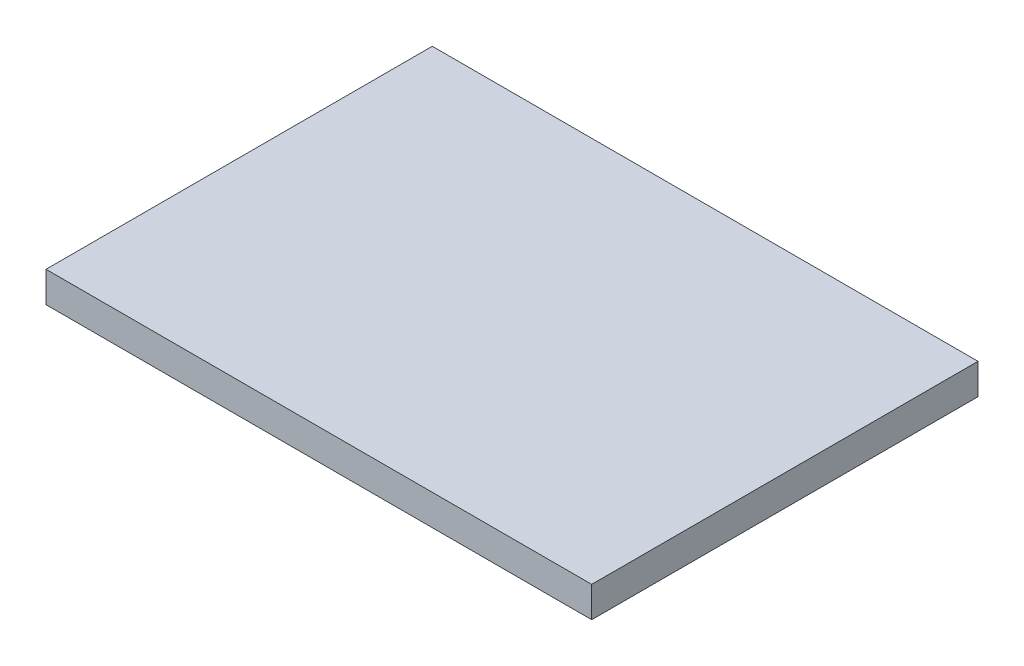
SolidWorks part; units mm, degrees
ref_plane "Front Plane" through (0, 0, 0) normal (0, 0, 1) x (1, 0, 0)
ref_plane "Top Plane" through (0, 0, 0) normal (0, 1, 0) x (1, 0, 0)
ref_plane "Right Plane" through (0, 0, 0) normal (1, 0, 0) x (0, 0, -1)
sketch "Sketch1" plane through (0, 0, 0) normal (0, 1, 0) x (1, 0, 0)
  line L1 (-17.8, -12.6) -> (17.8, -12.6)
  line L2 (-17.8, -12.6) -> (-17.8, 12.6)
  line L3 (-17.8, 12.6) -> (17.8, 12.6)
  line L4 (17.8, -12.6) -> (17.8, 12.6)
  line L5 (-17.8, -12.6) -> (17.8, 12.6) construction
  line L6 (-17.8, 12.6) -> (17.8, -12.6) construction
  point P0 (0, 0)
  dimension "D1" = 35.6
  dimension "D2" = 25.2
extrude "Boss-Extrude1" add sketch "Sketch1" along normal blind 2
